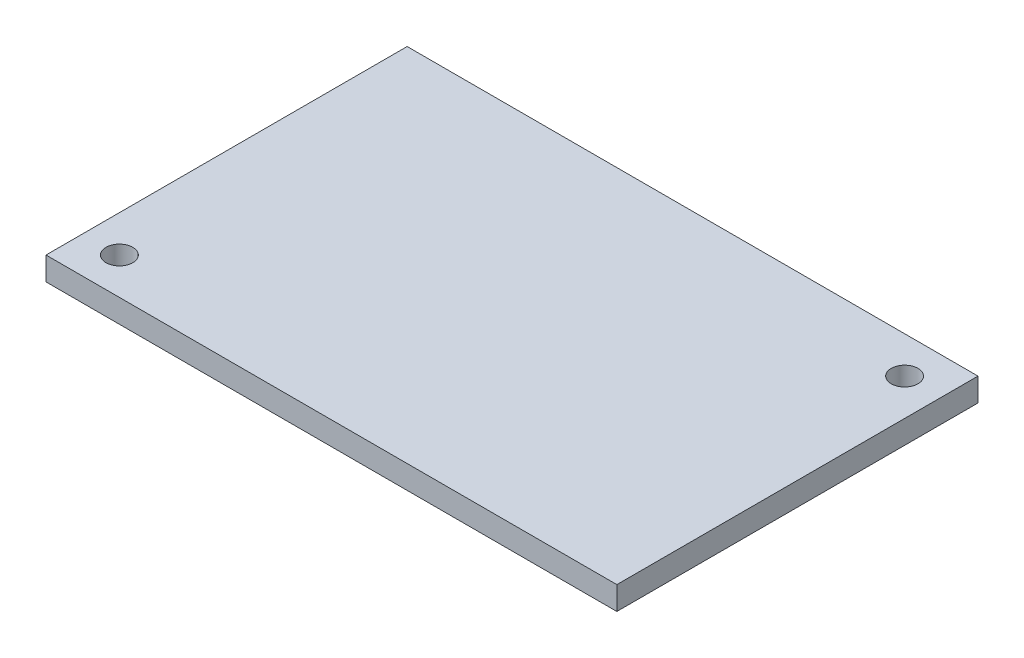
SolidWorks part; units mm, degrees
ref_plane "Front Plane" through (0, 0, 0) normal (0, 0, 1) x (1, 0, 0)
ref_plane "Top Plane" through (0, 0, 0) normal (0, 1, 0) x (1, 0, 0)
ref_plane "Right Plane" through (0, 0, 0) normal (1, 0, 0) x (0, 0, -1)
sketch "Sketch1" plane through (0, 0, 0) normal (0, 0, 1) x (1, 0, 0)
  line L1 (0, 0) -> (62.23, 0)
  line L2 (0, 0) -> (0, 2.54)
  line L3 (0, 2.54) -> (62.23, 2.54)
  line L4 (62.23, 0) -> (62.23, 2.54)
  dimension "D1" = 2.54
  dimension "D2" = 62.23
extrude "Boss-Extrude1" add sketch "Sketch1" against normal blind 39.37
sketch "Sketch2" plane through (0, 2.54, 0) normal (0, 1, 0) x (1, 0, 0)
  line L0 (0, 6.35) -> (6.35, 6.35)
  line L1 (0, 39.37) -> (0, 0) construction
  line L2 (6.35, 6.35) -> (6.35, 0)
  line L3 (62.23, 0) -> (0, 0) construction
  line L4 (55.88, 39.37) -> (55.88, 33.02)
  line L5 (62.23, 39.37) -> (0, 39.37) construction
  line L6 (62.23, 33.02) -> (55.88, 33.02)
  line L7 (62.23, 39.37) -> (62.23, 0) construction
  line L8 (45.212, 7.62) -> (45.212, 0) construction
  line L9 (42.164, 10.668) -> (33.401, 10.668) construction
  line L10 (30.353, 13.716) -> (30.353, 22.098) construction
  line L11 (48.26, 10.668) -> (62.23, 10.668) construction
  line L12 (33.2105, 24.384) -> (41.656, 24.384) construction
  line L13 (27.4955, 22.098) -> (33.2105, 22.098)
  line L14 (27.4955, 22.098) -> (27.4955, 26.67)
  line L15 (27.4955, 26.67) -> (33.2105, 26.67)
  line L16 (33.2105, 22.098) -> (33.2105, 26.67)
  line L21 (41.656, 22.2885) -> (48.768, 22.2885)
  line L22 (41.656, 22.2885) -> (41.656, 26.4795)
  line L23 (41.656, 26.4795) -> (48.768, 26.4795)
  line L24 (48.768, 22.2885) -> (48.768, 26.4795)
  circle A0 centre (4.0005, 4.0005) radius 1.4605
  circle A1 centre (58.2295, 35.3695) radius 1.4605
  circle A2 centre (45.212, 10.668) radius 3.048
  circle A3 centre (30.353, 10.668) radius 3.048
  point P34 (30.353, 22.098)
  point P41 (45.212, 22.2885)
  dimension "D9" = 2.921
  dimension "D12" = 6.096
  dimension "D1" = 6.35
  dimension "D2" = 6.35
  dimension "D3" = 6.35
  dimension "D4" = 6.35
  dimension "D5" = 2.3495
  dimension "D6" = 2.3495
  dimension "D7" = 2.3495
  dimension "D8" = 2.3495
  dimension "D10" = 7.62
  dimension "D11" = 13.97
  dimension "D13" = 8.763
  dimension "D14" = 8.382
  dimension "D15" = 5.715
  dimension "D16" = 4.572
  dimension "D17" = 4.191
  dimension "D18" = 7.112
extrude "Cut-Extrude1" cut sketch "Sketch2" against normal through all contours A0 | A1
